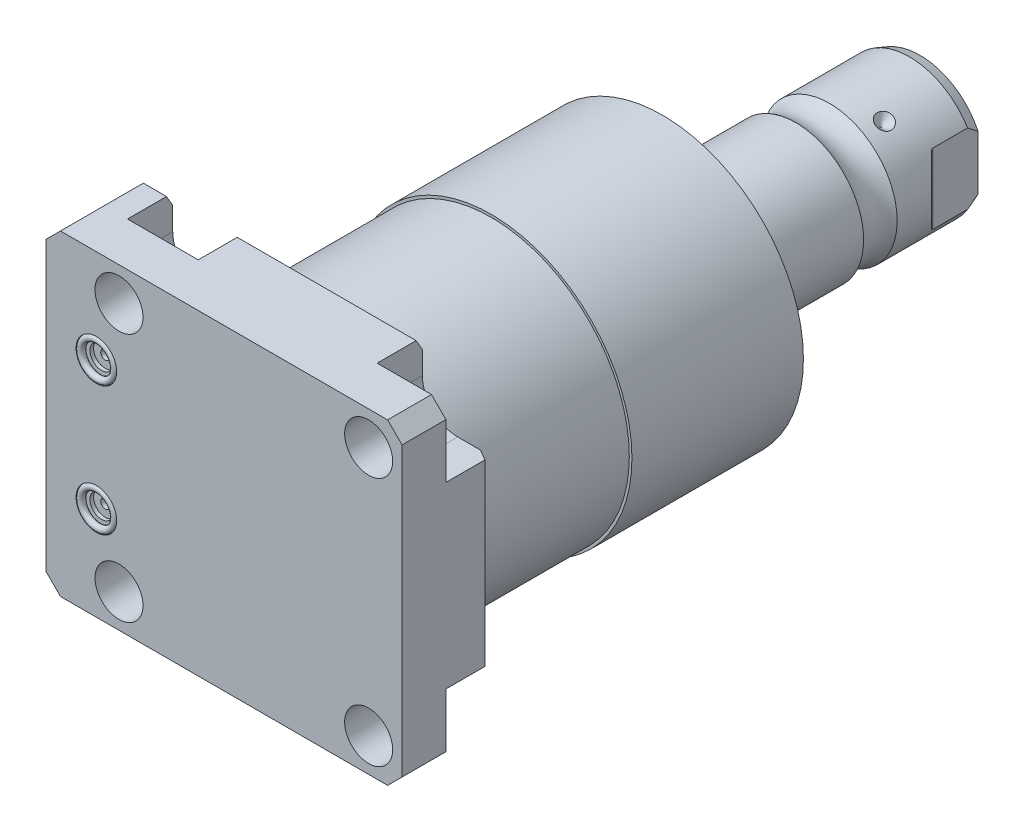
SolidWorks part; units mm, degrees
material "Alloy Steel"
ref_plane "Front Plane" through (0, 0, 0) normal (0, 0, 1) x (1, 0, 0)
ref_plane "Top Plane" through (0, 0, 0) normal (0, 1, 0) x (1, 0, 0)
ref_plane "Right Plane" through (0, 0, 0) normal (1, 0, 0) x (0, 0, -1)
sketch "Sketch1" plane through (0, 0, 0) normal (0, 0, 1) x (1, 0, 0)
  line L0 (-55.55, 44.45) -> (44.45, 44.45)
  line L1 (44.45, 44.45) -> (44.45, -44.45)
  line L2 (44.45, -44.45) -> (-55.55, -44.45)
  line L3 (-55.55, -44.45) -> (-55.55, 44.45)
  dimension "D1" = 100
  dimension "D2" = 88.9
  dimension "D3" = 44.45
  dimension "D4" = 44.45
extrude "Extrude1" add sketch "Sketch1" along normal blind 25.019
hole_wizard "Hole1" positions "Sketch22" profile "Sketch21" legacy end condition through all
sketch "Sketch22" plane through (0, 0, 0) normal (0, 0, -1) x (-1, 0, 0)
  line L0 (0, 0) -> (42.7441, 0) construction
  line L1 (0, 0.8532) -> (0, 27.5062) construction
  point P0 (-35.052, -35.052)
  point P9 (-35.052, 35.052)
  point P11 (35.052, 35.052)
  point P12 (35.052, -35.052)
  dimension "D1" = 35.052
  dimension "D2" = 35.052
sketch "Sketch21" plane through (35.052, -35.052, 0) normal (1, 0, 0) x (0, 1, 0)
  line L0 (0, 0) -> (0, 25.019)
  line L1 (0, 25.019) -> (6.7435, 25.019)
  line L2 (6.7435, 25.019) -> (6.7435, 0)
  line L3 (6.7435, 0) -> (0, 0)
  line L4 (0, 110) -> (0, -10) construction
  dimension "Diameter" = 13.487
  dimension "Depth" = 25.019
sketch "Sketch3" plane through (0, 0, 0) normal (0, 0, -1) x (-1, 0, 0)
  line L0 (-35.052, -25.1205) -> (-44.45, -25.1205)
  line L1 (-44.45, -44.45) -> (-44.45, -25.1205)
  line L2 (-44.45, 25.1205) -> (-44.45, 44.45)
  line L3 (-44.45, 25.1205) -> (-35.052, 25.1205)
  line L4 (-25.1205, 35.052) -> (-25.1205, 44.45)
  line L5 (-44.45, 44.45) -> (-25.1205, 44.45)
  line L6 (25.1205, 44.45) -> (25.1205, 35.052)
  line L7 (44.9835, 35.052) -> (44.9835, 44.45)
  line L8 (25.1205, 44.45) -> (44.9835, 44.45)
  line L9 (44.9835, -44.45) -> (25.1205, -44.45)
  line L10 (44.9835, -44.45) -> (44.9835, -35.052)
  line L11 (25.1205, -35.052) -> (25.1205, -44.45)
  line L12 (-25.1205, -44.45) -> (-44.45, -44.45)
  line L13 (-25.1205, -44.45) -> (-25.1205, -35.052)
  line L14 (-44.45, 44.45) -> (55.55, 44.45) construction
  line L15 (-44.45, -44.45) -> (-44.45, 44.45) construction
  line L16 (55.55, -44.45) -> (-44.45, -44.45) construction
  arc A0 (-25.1205, -35.052) -> (-35.052, -25.1205) centre (-35.052, -35.052) ccw
  arc A1 (-35.052, 25.1205) -> (-25.1205, 35.052) centre (-35.052, 35.052) ccw
  arc A2 (25.1205, 35.052) -> (44.9835, 35.052) centre (35.052, 35.052) ccw
  arc A3 (44.9835, -35.052) -> (25.1205, -35.052) centre (35.052, -35.052) ccw
  circle A8 centre (-35.052, 35.052) radius 6.7435 construction
  circle A9 centre (-35.052, -35.052) radius 6.7435 construction
  circle A10 centre (35.052, -35.052) radius 6.7435 construction
  circle A11 centre (35.052, 35.052) radius 6.7435 construction
  dimension "D1" = 9.9315
extrude "Cut-Extrude2" cut sketch "Sketch3" against normal blind 12.7
ref_plane "Plane16" through (0, 0, 12.014) normal (0, 0, 1) x (1, 0, 0)
sketch "Sketch23" plane through (0, 0, 12.014) normal (0, 0, 1) x (1, 0, 0)
  line L0 (-11.9397, -13.0048) -> (-61.0013, -13.0048) construction
  line L1 (-55.55, -23.749) -> (-55.296, -23.749)
  line L3 (-55.296, -23.749) -> (-55.296, -19.6596)
  line L4 (-55.296, -19.6596) -> (-54.5848, -18.9484)
  line L5 (-54.5848, -18.9484) -> (-41.1228, -18.9484)
  line L6 (-41.1228, -18.9484) -> (-41.1228, -13.0048)
  line L7 (-41.1228, -13.0048) -> (-55.55, -13.0048)
  line L8 (-55.55, -13.0048) -> (-55.55, -23.749)
  line L10 (-55.55, 44.45) -> (-55.55, -44.45) construction
  dimension "D1" = 21.4884
  dimension "D2" = 0.254
  dimension "D3" = 45
  dimension "D4" = 13.3096
  dimension "D5" = 11.8872
  dimension "D6" = 14.1732
  dimension "D7" = 13.0048
revolve "Cut-Revolve5" cut sketch "Sketch23" angle 360 about L0
mirror "Mirror1" about plane through (0, 0, 0) normal (0, 1, 0) of "Cut-Revolve5"
sketch "Sketch6" plane through (0, 0, 25.019) normal (0, 0, 1) x (1, 0, 0)
  line L0 (0, 0) -> (-71.0417, 0) construction
  circle A0 centre (-41.402, -18.11) radius 5.7023
  circle A1 centre (-41.402, 18.11) radius 5.7023
  dimension "D4" = 11.4046
  dimension "D1" = 18.11
  dimension "D2" = 36.22
  dimension "D3" = 41.402
extrude "Cut-Extrude3" cut sketch "Sketch6" against normal blind 1.4478
sketch "Sketch7" plane through (0, 0, 23.5712) normal (0, 0, 1) x (1, 0, 0)
  circle A0 centre (-41.402, 18.11) radius 3.2512
  circle A1 centre (-41.402, -18.11) radius 3.2512
  circle A2 centre (-41.402, 18.11) radius 5.7023 construction
  circle A3 centre (-41.402, -18.11) radius 5.7023 construction
  dimension "D1" = 6.5024
extrude "Cut-Extrude4" cut sketch "Sketch7" against normal blind 1.016
sketch "Sketch8" plane through (0, 0, 22.5552) normal (0, 0, 1) x (1, 0, 0)
  circle A0 centre (-41.402, 18.11) radius 1.2446
  circle A1 centre (-41.402, -18.11) radius 1.2446
  circle A2 centre (-41.402, 18.11) radius 5.7023 construction
  circle A3 centre (-41.402, -18.11) radius 5.7023 construction
  dimension "D1" = 2.4892
extrude "Cut-Extrude5" cut sketch "Sketch8" against normal blind 11.9888
ref_plane "Plane17" through (0, 18.11, 0) normal (0, 1, 0) x (-1, 0, 0)
sketch "Sketch9" plane through (-41.656, 18.11, 23.5712) normal (0, 1, 0) x (1, 0, 0)
  line L0 (0.254, -1.9469) -> (0.254, 0.0927) construction
  line L3 (-5.4483, 0) -> (5.9563, 0) construction
  line L4 (0.254, 13.0048) -> (0.254, 1.016) construction
  circle A0 centre (5.0292, -0.9271) radius 0.9271
  dimension "D1" = 1.8542
  dimension "D2" = 9.5504
revolve "Revolve1" add sketch "Sketch9" angle 360 about L0
mirror "Mirror2" about plane through (0, 0, 0) normal (0, 1, 0) of bodies 116
chamfer "Chamfer1" distance 4.064 angle 45 4 edges at (44.45, -44.45, 18.8595) (44.45, 44.45, 18.8595) (-55.55, 44.45, 12.5095) (-55.55, -44.45, 12.5095)
chamfer "Chamfer2" distance 3.0226 angle 30 5 edges at (-48.2347, -44.45, 0) (0, -44.45, 0) (44.45, 0, 0) (-48.2347, 44.45, 0) (0, 44.45, 0)
sketch "Sketch24" plane through (0, 0, 0) normal (1, 0, 0) x (0, 0, -1)
  line L0 (0, 0) -> (113.9127, 0) construction
  line L1 (0, 0) -> (0, 38.786)
  line L2 (0, 38.786) -> (44.45, 38.786)
  line L3 (44.45, 38.786) -> (44.45, 39.5225)
  line L4 (44.45, 39.5225) -> (92.6089, 39.5225)
  line L5 (92.6089, 39.5225) -> (96.393, 25.4)
  line L6 (96.393, 25.4) -> (96.393, 0)
  line L7 (96.393, 0) -> (0, 0)
  dimension "D1" = 77.572
  dimension "D2" = 44.45
  dimension "D3" = 79.045
  dimension "D4" = 50.8
  dimension "D5" = 15
  dimension "D6" = 96.393
revolve "Revolve4" add sketch "Sketch24" angle 360 about L0
sketch "Sketch17" plane through (0, 0, 0) normal (1, 0, 0) x (0, 0, -1)
  line L0 (96.393, 0) -> (96.393, -19.05)
  line L1 (96.393, -19.05) -> (129.9899, -19.05)
  line L2 (139.4041, -19.05) -> (161.951, -19.05)
  line L3 (164.872, -17.9868) -> (164.872, 0)
  line L4 (164.872, 0) -> (96.393, 0)
  line L5 (130.8989, 0) -> (0.816, 0) construction
  line L6 (96.393, -25.4) -> (96.393, 25.4) construction
  line L7 (-25.019, -40.386) -> (-25.019, 40.386) construction
  line L8 (164.872, -17.9868) -> (161.951, -19.05)
  arc A0 (139.4041, -19.05) -> (129.9899, -19.05) centre (134.697, -25.4254) ccw
  dimension "D2" = 20
  dimension "D4" = 7.9248
  dimension "D5" = 35.0012
  dimension "D1" = 189.891
  dimension "D3" = 38.1
  dimension "D6" = 30.175
  dimension "D7" = 2.921
revolve "Revolve3" add sketch "Sketch17" angle 360 about L5
sketch "Sketch28" plane through (0, 0, 0) normal (0, 1, 0) x (1, 0, 0)
  line L0 (-34.3062, 145.365) -> (35.4095, 145.365) construction
  line L1 (-19.05, 147.778) -> (-16.637, 145.365)
  line L2 (-19.05, 161.951) -> (-19.05, 139.4041) construction
  line L3 (-16.637, 145.365) -> (-19.05, 145.365)
  line L4 (-19.05, 145.365) -> (-19.05, 147.778)
  arc A0 (-19.05, 129.9899) -> (-19.05, 139.4041) centre (-25.4254, 134.697) ccw construction
  dimension "D3" = 10.668
  dimension "D1" = 45
  dimension "D2" = 4.826
revolve "Cut-Revolve6" cut sketch "Sketch28" angle 360 about L0
pattern_circular "CirPattern1" count 3 over 360 about axis through (0, 0, -130.8989) along (0, 0, -1) of "Cut-Revolve6"
hole_wizard "Hole2" positions "Sketch33" profile "Sketch32" legacy
sketch "Sketch33" plane through (0, 0, -164.872) normal (0, 0, -1) x (-1, 0, 0)
  circle A0 centre (0, 0) radius 19.05 construction
  point P0 (0, 0)
sketch "Sketch32" plane through (0, 0, -164.872) normal (1, 0, 0) x (0, 1, 0)
  line L0 (0, 0) -> (0, 29.5665)
  line L1 (0, 29.5665) -> (6.9342, 25.4)
  line L2 (6.9342, 25.4) -> (6.9342, 0)
  line L4 (6.9342, 0) -> (0, 0)
  line L6 (0, 29.5665) -> (-6.9342, 25.4) construction
  line L7 (0, -4.2442) -> (0, 117.3081) construction
  dimension "Diameter" = 13.8684
  dimension "Depth" = 25.4
  dimension "Drill Angle" = 118
sketch "Sketch34" plane through (0, 0, 0) normal (0, 1, 0) x (0, 0, -1)
  line L0 (0, 0) -> (211.3651, 0) construction
  line L1 (149.0879, 19.05) -> (151.6332, 16.5047)
  line L3 (152.172, 16.2815) -> (164.872, 16.2815)
  line L4 (164.872, -17.9868) -> (164.872, 17.9868) construction
  line L5 (164.872, 16.2815) -> (164.872, 19.05)
  line L6 (164.872, 19.05) -> (149.0879, 19.05)
  line L7 (164.872, -19.05) -> (149.0879, -19.05)
  line L8 (164.872, -16.2815) -> (164.872, -19.05)
  line L9 (152.172, -16.2815) -> (164.872, -16.2815)
  line L10 (149.0879, -19.05) -> (151.6332, -16.5047)
  line L11 (161.951, 19.05) -> (147.778, 19.05) construction
  arc A0 (152.172, 16.2815) -> (151.6332, 16.5047) centre (152.172, 17.0435) cw
  arc A1 (152.172, -16.2815) -> (151.6332, -16.5047) centre (152.172, -17.0435) ccw
  dimension "D2" = 0.762
  dimension "D1" = 45
  dimension "D3" = 12.7
  dimension "D4" = 32.563
extrude "Cut-Extrude8" cut sketch "Sketch34" against normal through all and the other way through all
